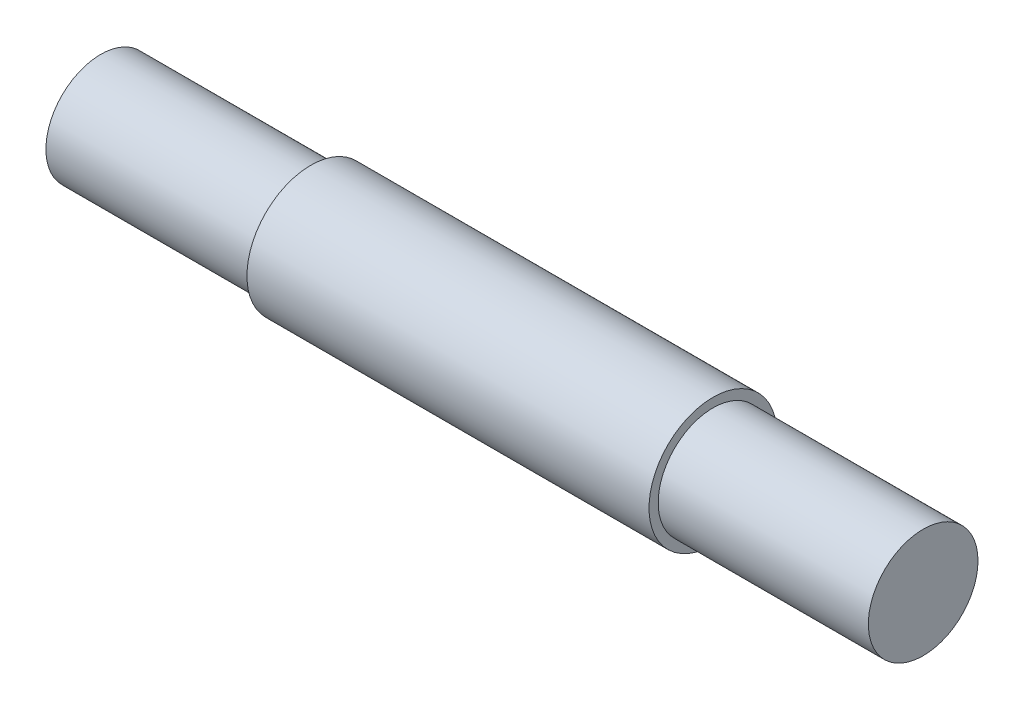
SolidWorks part; units mm, degrees
material "Brass"
ref_plane "Front Plane" through (0, 0, 0) normal (0, 0, 1) x (1, 0, 0)
ref_plane "Top Plane" through (0, 0, 0) normal (0, 1, 0) x (1, 0, 0)
ref_plane "Right Plane" through (0, 0, 0) normal (1, 0, 0) x (0, 0, -1)
sketch "Sketch1" plane through (0, 0, 0) normal (1, 0, 0) x (0, 0, -1)
  circle A0 centre (0, 0) radius 4.445
  dimension "D1" = 8.89
extrude "Boss-Extrude1" add sketch "Sketch1" along normal mid plane 57.15
sketch "Sketch2" plane through (28.575, 0, 0) normal (1, 0, 0) x (0, 0, -1)
  circle A0 centre (0, 0) radius 3.81
  circle A1 centre (0, 0) radius 4.445 construction
  dimension "D1" = 7.62
extrude "Cut-Extrude-Thin1" cut sketch "Sketch2" against normal blind 14.605 thin
mirror "Mirror1" about plane through (0, 0, 0) normal (1, 0, 0) of "Cut-Extrude-Thin1"
